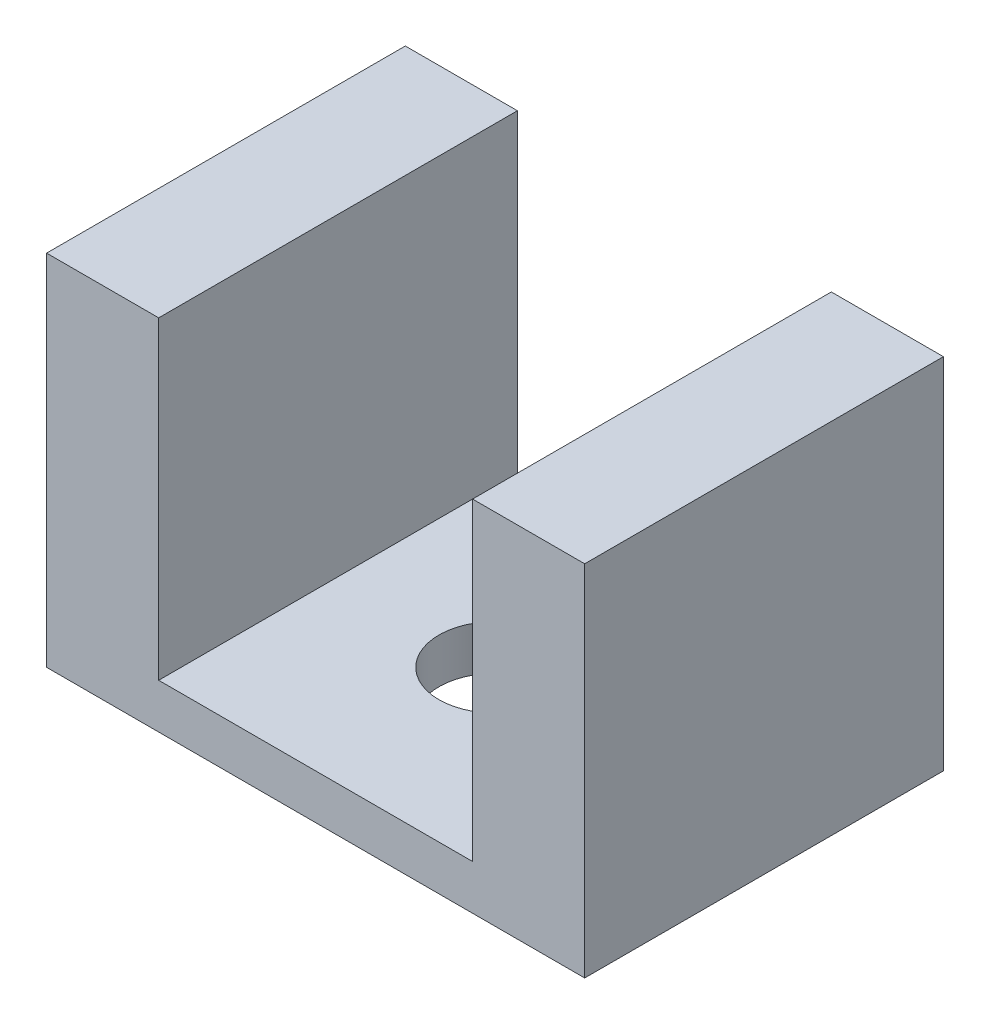
SolidWorks part; units mm, degrees
material "6063-O"
ref_plane "Front" through (0, 0, 0) normal (0, 0, 1) x (1, 0, 0)
ref_plane "Top" through (0, 0, 0) normal (0, 1, 0) x (1, 0, 0)
ref_plane "Right" through (0, 0, 0) normal (1, 0, 0) x (0, 0, -1)
sketch "Sketch1" plane through (0, 0, 0) normal (0, 0, 1) x (1, 0, 0)
  line L0 (0, 0) -> (0, 61400.5293) construction
  line L1 (22.225, 0) -> (-22.225, 0)
  line L2 (-22.225, 0) -> (-22.225, 44.45)
  line L3 (-22.225, 44.45) -> (-38.1, 44.45)
  line L4 (-38.1, 44.45) -> (-38.1, -6.35)
  line L5 (-38.1, -6.35) -> (38.1, -6.35)
  line L6 (38.1, 44.45) -> (38.1, -6.35)
  line L7 (22.225, 0) -> (22.225, 44.45)
  line L8 (22.225, 44.45) -> (38.1, 44.45)
  point P13 (0, 0)
  point P14 (0, -6.35)
  dimension "D1" = 15.875
  dimension "D2" = 50.8
  dimension "D3" = 6.35
  dimension "D4" = 38.1
extrude "Boss-Extrude1" add sketch "Sketch1" along normal blind 50.8
sketch "Sketch2" plane through (0, 0, 0) normal (0, 1, 0) x (1, 0, 0)
  line L0 (0, 0) -> (0, -50.8) construction
  line L1 (22.225, -50.8) -> (-22.225, -50.8) construction
  circle A0 centre (0, -25.4) radius 7.9375
  dimension "D1" = 15.875
extrude "Cut-Extrude1" cut sketch "Sketch2" against normal through all
